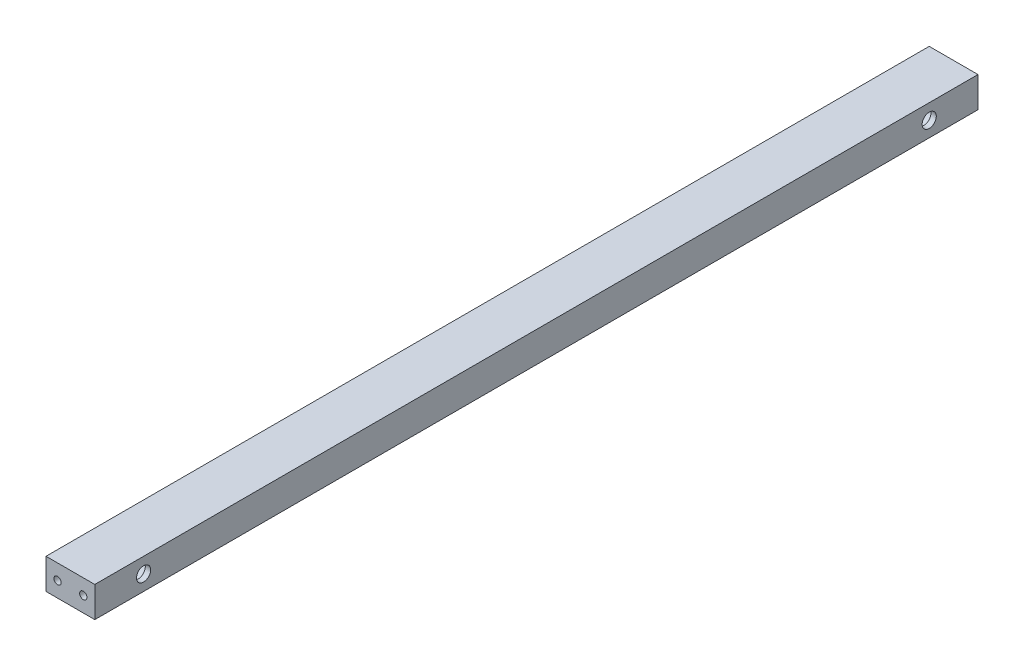
SolidWorks part; units mm, degrees
ref_plane "Front Plane" through (0, 0, 0) normal (0, 0, 1) x (1, 0, 0)
ref_plane "Top Plane" through (0, 0, 0) normal (0, 1, 0) x (1, 0, 0)
ref_plane "Right Plane" through (0, 0, 0) normal (1, 0, 0) x (0, 0, -1)
sketch "Sketch1" plane through (0, 0, 0) normal (0, 0, 1) x (1, 0, 0)
  line L1 (0, 0) -> (25.4, 0)
  line L2 (0, 0) -> (0, 15.875)
  line L3 (0, 15.875) -> (25.4, 15.875)
  line L4 (25.4, 0) -> (25.4, 15.875)
  dimension "D1" = 25.4
  dimension "D2" = 15.875
extrude "Boss-Extrude1" add sketch "Sketch1" along normal blind 459.74
sketch "Sketch8" plane through (0, 0, 0) normal (-1, 0, 0) x (0, 0, 1)
  line L0 (459.74, 7.9375) -> (0, 7.9375) construction
  line L1 (459.74, 15.875) -> (459.74, 0) construction
  line L2 (0, 15.875) -> (0, 0) construction
  line L3 (229.87, 15.875) -> (229.87, 0) construction
  line L4 (459.74, 15.875) -> (0, 15.875) construction
  line L5 (459.74, 0) -> (0, 0) construction
  circle A0 centre (434.34, 7.9375) radius 6.8199
  circle A1 centre (25.4, 7.9375) radius 6.8199
  dimension "D1" = 25.4
extrude "Cut-Extrude1" cut sketch "Sketch8" against normal blind 22.6136
hole_wizard "L (0.29) Diameter Hole1" positions "Sketch10" profile "Sketch9" hole size "L" standard "ANSI Inch"
sketch "Sketch10" plane through (22.6136, 0, 0) normal (-1, 0, 0) x (0, 0, 1)
  point P0 (25.4, 7.9375)
  point P3 (434.34, 7.9375)
sketch "Sketch9" plane through (22.6136, 7.9375, 25.4) normal (0, 1, 0) x (0, 0, 1)
  line L0 (0, 0) -> (0, 53.013)
  line L1 (0, 53.013) -> (3.683, 50.8)
  line L2 (3.683, 50.8) -> (3.683, 0)
  line L5 (3.683, 0) -> (0, 0)
  line L10 (0, 53.013) -> (-3.683, 50.8) construction
  line L11 (0, -6.35) -> (0, 107.95) construction
  dimension "Hole Dia." = 7.366
  dimension "Hole Depth" = 50.8
  dimension "Drill Angle" = 118
hole_wizard "Tap Drill for #10-24 Tap2" positions "Sketch15" profile "Sketch16" hole size "#10-24" standard "ANSI Inch"
sketch "Sketch15" plane through (-2202.6381, 879.5991, 459.74) normal (0, 0, 1) x (0, 1, 0)
  line L0 (-863.7241, -2202.6381) -> (-879.5991, -2202.6381) construction
  line L1 (-879.5991, -2228.0381) -> (-863.7241, -2228.0381) construction
  point P1 (-871.6616, -2222.0381)
  point P3 (-871.6616, -2208.6381)
  dimension "D1" = 6
  dimension "D2" = 6
sketch "Sketch16" plane through (19.4, 7.9375, 459.74) normal (1, 0, 0) x (0, -1, 0)
  line L0 (0, 0) -> (0, 21.8418)
  line L1 (0, 21.8418) -> (1.8986, 20.701)
  line L2 (1.8986, 20.701) -> (1.8986, 0)
  line L3 (1.8986, 0) -> (0, 0)
  line L4 (0, 21.8418) -> (-1.8987, 20.701) construction
  line L5 (0, -6.35) -> (0, 107.95) construction
  dimension "Hole Dia." = 3.7973
  dimension "Hole Depth" = 20.701
  dimension "Drill Angle" = 118
hole_wizard "Tap Drill for #10-24 Tap1" positions "Sketch20" profile "Sketch19" hole size "#10-24" standard "ANSI Inch"
sketch "Sketch20" plane through (0, 0, 0) normal (0, 0, -1) x (-1, 0, 0)
  line L0 (-25.4, 0) -> (-25.4, 15.875) construction
  line L1 (0, 15.875) -> (0, 0) construction
  point P0 (-19.4, 7.9375)
  point P2 (-6, 7.9375)
  point P5 (-25.4, 7.9375)
  point P8 (0, 7.9375)
  dimension "D1" = 6
  dimension "D2" = 6
sketch "Sketch19" plane through (19.4, 7.9375, 0) normal (1, 0, 0) x (0, 1, 0)
  line L0 (0, 0) -> (0, 21.8418)
  line L1 (0, 21.8418) -> (1.8986, 20.701)
  line L2 (1.8986, 20.701) -> (1.8986, 0)
  line L5 (1.8986, 0) -> (0, 0)
  line L10 (0, 21.8418) -> (-1.8987, 20.701) construction
  line L11 (0, -6.35) -> (0, 107.95) construction
  dimension "Hole Dia." = 3.7973
  dimension "Hole Depth" = 20.701
  dimension "Drill Angle" = 118
